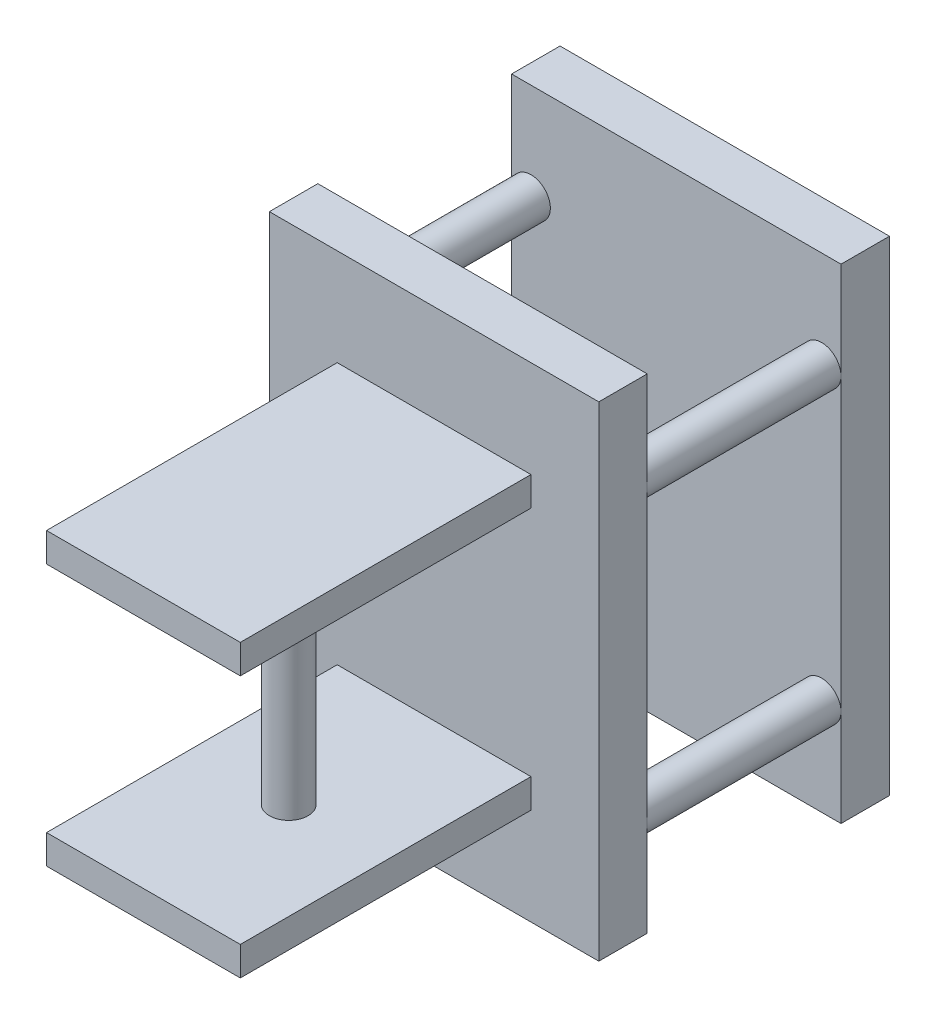
SolidWorks part; units mm, degrees
ref_plane "前视基准面" through (0, 0, 0) normal (0, 0, 1) x (1, 0, 0)
ref_plane "上视基准面" through (0, 0, 0) normal (0, 1, 0) x (1, 0, 0)
ref_plane "右视基准面" through (0, 0, 0) normal (1, 0, 0) x (0, 0, -1)
sketch "草图1" plane through (0, 0, 0) normal (0, 0, 1) x (1, 0, 0)
  line L13 (-21.9493, 41.9997) -> (12.0507, 41.9997)
  line L14 (-21.9493, 41.9997) -> (-21.9493, -8.0003)
  line L15 (-21.9493, -8.0003) -> (12.0507, -8.0003)
  line L16 (12.0507, 41.9997) -> (12.0507, -8.0003)
  dimension "D1" = 50
  dimension "D2" = 34
extrude "凸台-拉伸1" add sketch "草图1" along normal blind 5
sketch "草图2" plane through (0, 0, 5) normal (0, 0, 1) x (1, 0, 0)
  line L0 (-4.9493, 41.9997) -> (-4.9493, -8.0003) construction
  line L1 (-21.9493, 41.9997) -> (12.0507, 41.9997)
  line L2 (-21.9493, 41.9997) -> (-21.9493, -8.0003)
  line L3 (-21.9493, -8.0003) -> (12.0507, -8.0003)
  line L4 (12.0507, 41.9997) -> (12.0507, -8.0003)
  line L5 (-14.9493, 41.9997) -> (5.0507, 41.9997)
  line L6 (-14.9493, 41.9997) -> (-14.9493, -8.0003)
  line L7 (-14.9493, -8.0003) -> (5.0507, -8.0003)
  line L8 (5.0507, 41.9997) -> (5.0507, -8.0003)
  line L9 (-21.9493, 16.9997) -> (12.0507, 16.9997) construction
  circle A0 centre (-19.9493, 31.9997) radius 2
  circle A1 centre (10.0507, 31.9997) radius 2
  circle A2 centre (10.0507, 1.9997) radius 2
  circle A3 centre (-19.9493, 1.9997) radius 2
  dimension "D5" = 4
  dimension "D1" = 0
  dimension "D2" = 7
  dimension "D3" = 20
  dimension "D4" = 50
  dimension "D6" = 10
  dimension "D7" = 2
extrude "凸台-拉伸2" add sketch "草图2" along normal blind 20 contours A0 | A3 | A1 | A2
sketch "草图3" plane through (0, 0, 25) normal (0, 0, 1) x (1, 0, 0)
  line L1 (-21.9493, 42.1946) -> (12.0507, 42.1946)
  line L2 (-21.9493, 42.1946) -> (-21.9493, -7.8054)
  line L3 (-21.9493, -7.8054) -> (12.0507, -7.8054)
  line L4 (12.0507, 42.1946) -> (12.0507, -7.8054)
  circle A1 centre (-19.9493, 31.9997) radius 2 construction
  dimension "D3" = 2
  dimension "D1" = 50
  dimension "D2" = 34
extrude "凸台-拉伸3" add sketch "草图3" along normal blind 5
sketch "草图4" plane through (0, 0, 30) normal (0, 0, 1) x (1, 0, 0)
  line L1 (-14.9493, 29.1946) -> (5.0507, 29.1946)
  line L3 (-14.9493, 5.1946) -> (5.0507, 5.1946)
  line L5 (12.0507, 42.1946) -> (-21.9493, 42.1946) construction
  line L6 (-21.9493, 42.1946) -> (-21.9493, -7.8054) construction
  line L7 (-14.9493, 29.1946) -> (5.0507, 29.1946)
  line L8 (-14.9493, 29.1946) -> (-14.9493, 32.1946)
  line L9 (-14.9493, 32.1946) -> (5.0507, 32.1946)
  line L10 (5.0507, 29.1946) -> (5.0507, 32.1946)
  line L11 (-14.9493, 5.1946) -> (5.0507, 5.1946)
  line L12 (-14.9493, 5.1946) -> (-14.9493, 2.1946)
  line L13 (-14.9493, 2.1946) -> (5.0507, 2.1946)
  line L14 (5.0507, 5.1946) -> (5.0507, 2.1946)
  dimension "D1" = 20
  dimension "D2" = 24
  dimension "D3" = 7
  dimension "D4" = 13
  dimension "D5" = 3
  dimension "D6" = 3
extrude "凸台-拉伸4" add sketch "草图4" along normal blind 30 contours L1 L10 L9 L8 | L14 L3 L12 L13
sketch "草图5" plane through (0, 5.1946, 0) normal (0, 1, 0) x (1, 0, 0)
  line L0 (-14.9493, -60) -> (-14.9493, -30) construction
  line L2 (-14.9493, -60) -> (5.0507, -60) construction
  circle A0 centre (-4.9493, -45) radius 2
  point P6 (-5.1153, -60)
  point P7 (-42.0504, -31.7613)
  dimension "D1" = 10
  dimension "D2" = 15
extrude "凸台-拉伸5" add sketch "草图5" along normal blind 25
